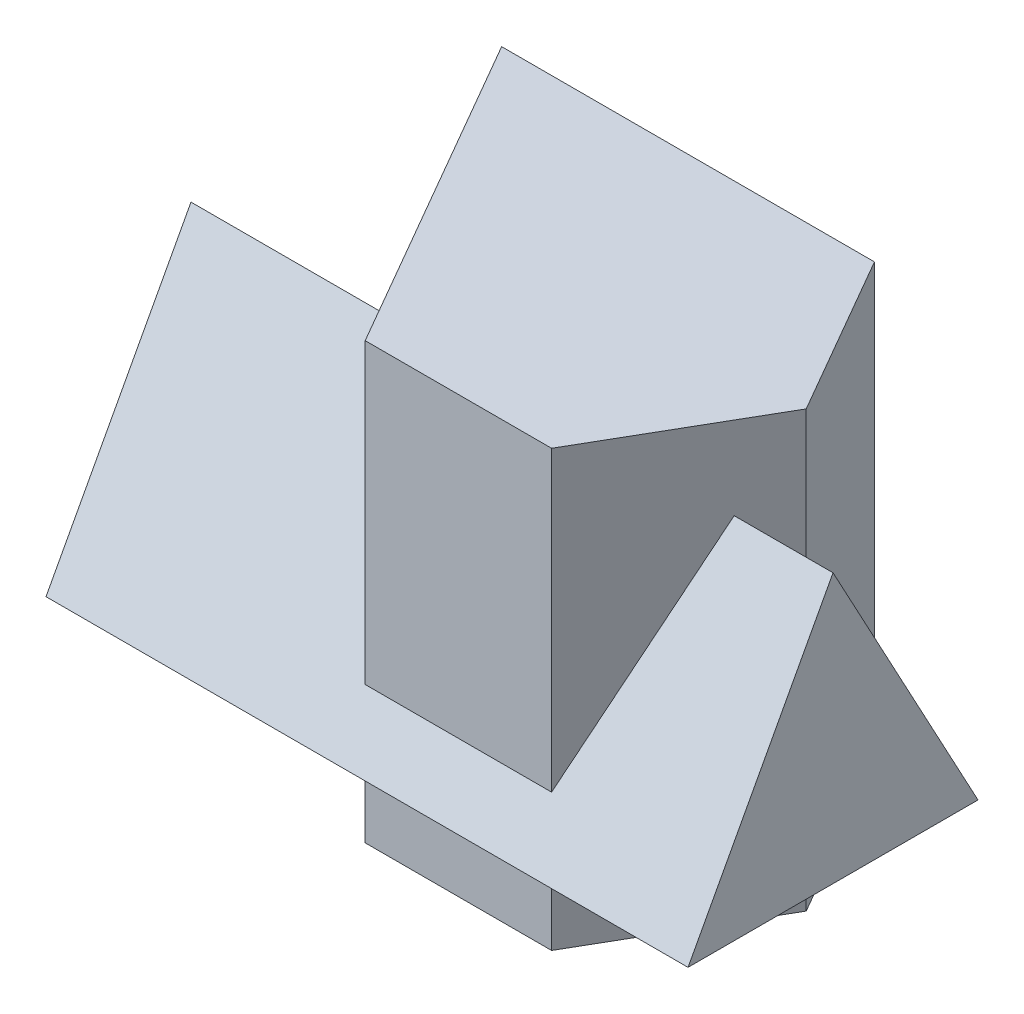
SolidWorks part; units mm, degrees
ref_plane "Front" through (0, 0, 0) normal (0, 0, 1) x (1, 0, 0)
ref_plane "Top" through (0, 0, 0) normal (0, 1, 0) x (1, 0, 0)
ref_plane "Right" through (0, 0, 0) normal (1, 0, 0) x (0, 0, -1)
sketch "Sketch1" plane through (0, 0, 0) normal (0, 1, 0) x (1, 0, 0)
  line L1 (45, 0) -> (22.5, 38.9711)
  line L2 (22.5, 38.9711) -> (-67.5, 38.9711)
  line L4 (-67.5, 38.9711) -> (-22.5, -38.9711)
  line L5 (-22.5, -38.9711) -> (22.5, -38.9711)
  line L6 (22.5, -38.9711) -> (45, 0)
  line L7 (-22.5, 38.9711) -> (-45, 0) [skipped]
extrude "Extrude1" add sketch "Sketch1" along normal blind 105
sketch "Sketch2" plane through (0, 0, 0) normal (1, 0, 0) x (0, 0, -1)
  line L1 (-46.0289, 20) -> (23.9711, 20)
  line L8 (-46.0289, 20) -> (-11.0289, 85)
  line L9 (-11.0289, 85) -> (23.9711, 20)
extrude "Extrude2" add sketch "Sketch2" against normal blind 155 from offset 62.5 separate body
